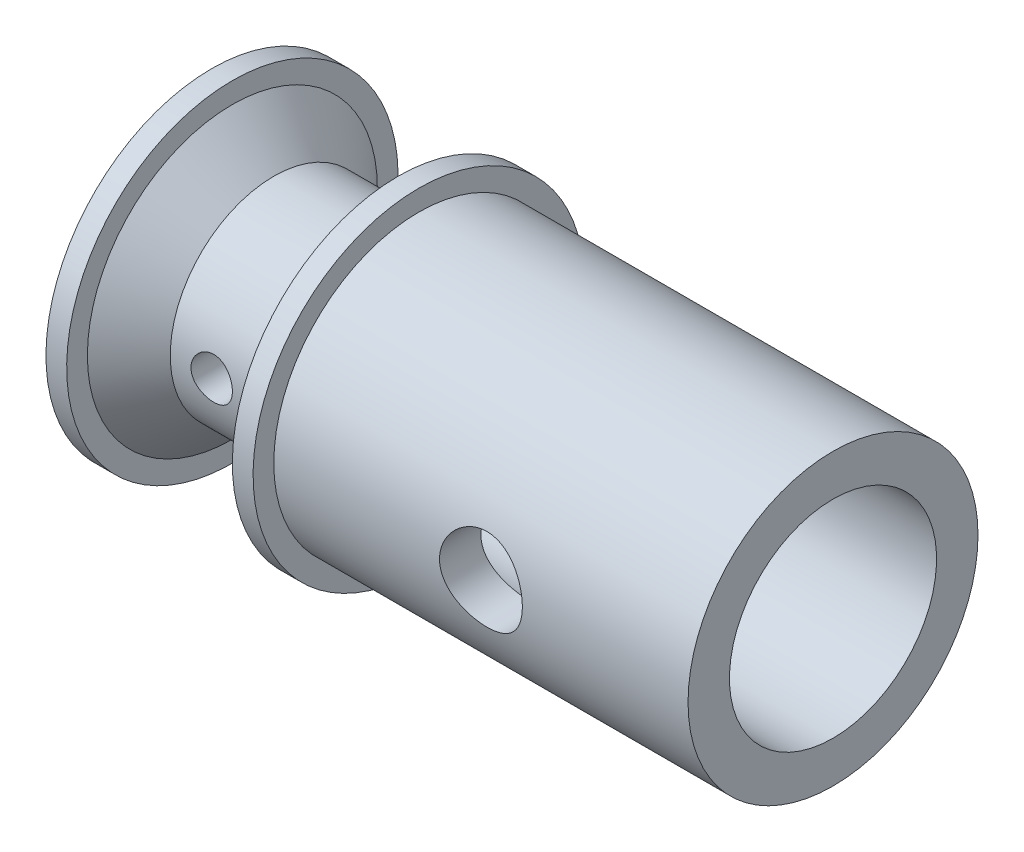
SolidWorks part; units mm, degrees
ref_plane "Front Plane" through (0, 0, 0) normal (0, 0, 1) x (1, 0, 0)
ref_plane "Top Plane" through (0, 0, 0) normal (0, 1, 0) x (1, 0, 0)
ref_plane "Right Plane" through (0, 0, 0) normal (1, 0, 0) x (0, 0, -1)
sketch "Sketch1" plane through (0, 0, 0) normal (0, 0, 1) x (1, 0, 0)
  line L0 (0, 0) -> (0, 2.5)
  line L1 (0, 2.5) -> (10, 2.5)
  line L2 (10, 2.5) -> (10, 3.5)
  line L3 (10, 3.5) -> (0, 3.5)
  line L4 (0, 3.5) -> (0, 4)
  line L5 (-0.5, 4) -> (-0.5, 3.5)
  line L6 (-0.5, 3.5) -> (-1.5, 2.5)
  line L7 (-1.5, 2.5) -> (-3.5, 2.5)
  line L8 (-3.5, 2.5) -> (-4.5, 3.5)
  line L9 (-4.5, 3.5) -> (-4.5, 4)
  line L10 (-4.5, 4) -> (-5, 4)
  line L11 (-5, 4) -> (-5, 0)
  line L12 (0, 4) -> (-0.5, 4)
  line L13 (0, 0) -> (-5, 0)
  dimension "D1" = 1
  dimension "D2" = 10
  dimension "D3" = 2.5
  dimension "D4" = 2.5
  dimension "D5" = 45
  dimension "D6" = 0.5
  dimension "D7" = 0.5
  dimension "D8" = 4
  dimension "D9" = 1
  dimension "D10" = 1
  dimension "D11" = 4
  dimension "D12" = 4
revolve "Revolve1" add sketch "Sketch1" angle 360 about L13
sketch "Sketch3" plane through (0, 0, 0) normal (0, 0, 1) x (1, 0, 0)
  line L0 (-3, 0) -> (6, 0) construction
  circle A0 centre (-2.5, 0) radius 0.5
  circle A1 centre (5, 0) radius 1
  dimension "D3" = 1
  dimension "D4" = 2
  dimension "D1" = 2.5
  dimension "D2" = 5
extrude "Cut-Extrude1" cut sketch "Sketch3" against normal through all both and the other way through all contours A1 | A0
